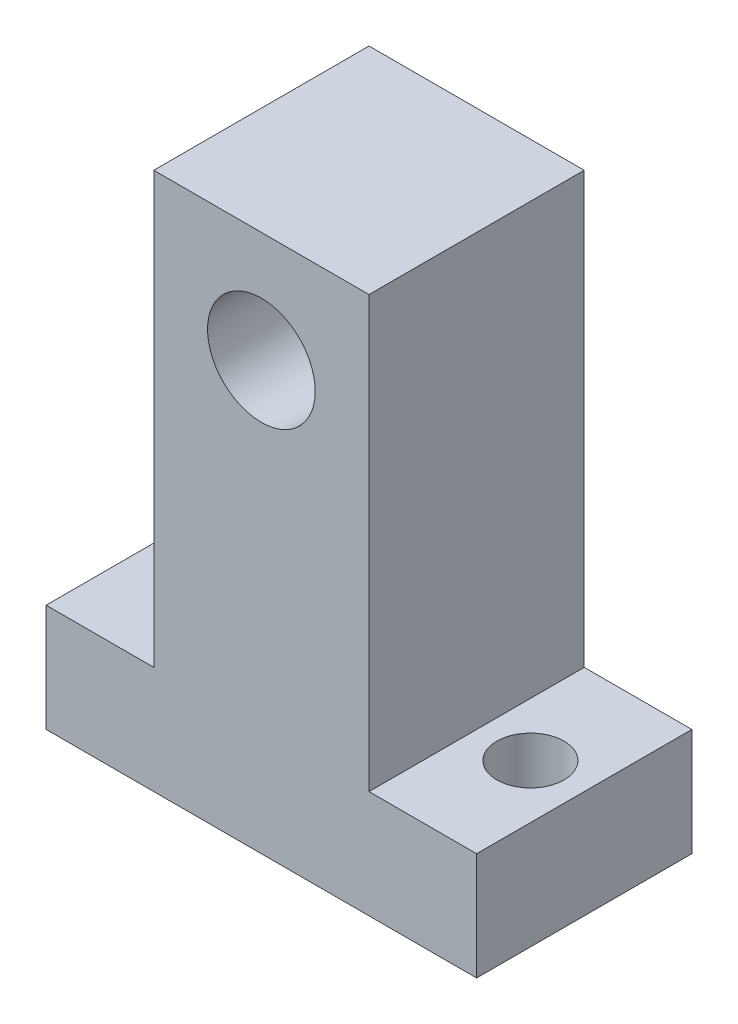
SolidWorks part; units mm, degrees
ref_plane "前视基准面" through (0, 0, 0) normal (0, 0, 1) x (1, 0, 0)
ref_plane "上视基准面" through (0, 0, 0) normal (0, 1, 0) x (1, 0, 0)
ref_plane "右视基准面" through (0, 0, 0) normal (1, 0, 0) x (0, 0, -1)
sketch "草图1" plane through (0, 0, 0) normal (0, 0, 1) x (1, 0, 0)
  line L0 (0, 0) -> (16, 0)
  line L1 (16, 0) -> (16, 8)
  line L2 (16, 8) -> (8, 8)
  line L3 (8, 8) -> (8, 40)
  line L4 (8, 40) -> (-8, 40)
  line L5 (-8, 40) -> (-8, 8)
  line L6 (-8, 8) -> (-16, 8)
  line L7 (-16, 8) -> (-16, 0)
  line L8 (-16, 0) -> (0, 0)
  dimension "D1" = 16
  dimension "D2" = 16
  dimension "D3" = 8
  dimension "D4" = 8
  dimension "D5" = 32
  dimension "D6" = 16
  dimension "D7" = 8
extrude "凸台-拉伸1" add sketch "草图1" along normal blind 16
sketch "草图2" plane through (0, 8, 0) normal (0, 1, 0) x (1, 0, 0)
  line L0 (-16, -16) -> (-16, 0) construction
  line L1 (-8, 0) -> (-16, 0) construction
  line L2 (0, 0) -> (0, -4.2655)
  circle A0 centre (-12, -8) radius 2.5
  circle A1 centre (12, -8) radius 2.5
  dimension "D1" = 5
  dimension "D2" = 4
  dimension "D3" = 8
extrude "切除-拉伸1" cut sketch "草图2" against normal through all contours A0 | A1
sketch "草图3" plane through (0, 0, 16) normal (0, 0, 1) x (1, 0, 0)
  circle A0 centre (0, 31.77) radius 4
extrude "切除-拉伸2" cut sketch "草图3" against normal blind 29
